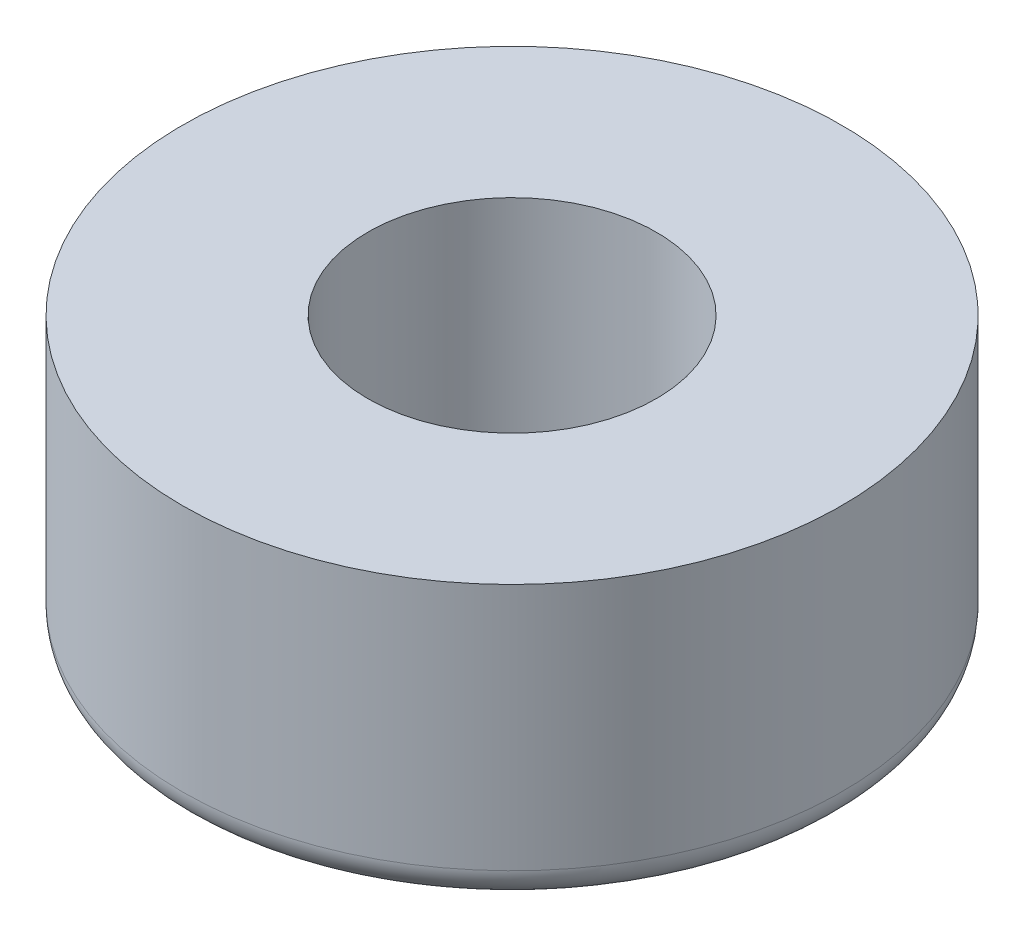
SolidWorks part; units mm, degrees
ref_plane "Front Plane" through (0, 0, 0) normal (0, 0, 1) x (1, 0, 0)
ref_plane "Top Plane" through (0, 0, 0) normal (0, 1, 0) x (1, 0, 0)
ref_plane "Right Plane" through (0, 0, 0) normal (1, 0, 0) x (0, 0, -1)
sketch "Sketch1" plane through (0, 0, 0) normal (0, 1, 0) x (1, 0, 0)
  circle A0 centre (0, 0) radius 3.475
  circle A1 centre (0, 0) radius 7.9375
  dimension "D1" = 15.875
  dimension "D2" = 6.95
extrude "Boss-Extrude1" add sketch "Sketch1" along normal blind 6.731
fillet "Fillet1" radius 0.76 1 edges at (0, 0, 7.9375)
equation "\"D2@Sketch1\"=.25+.6mm"
